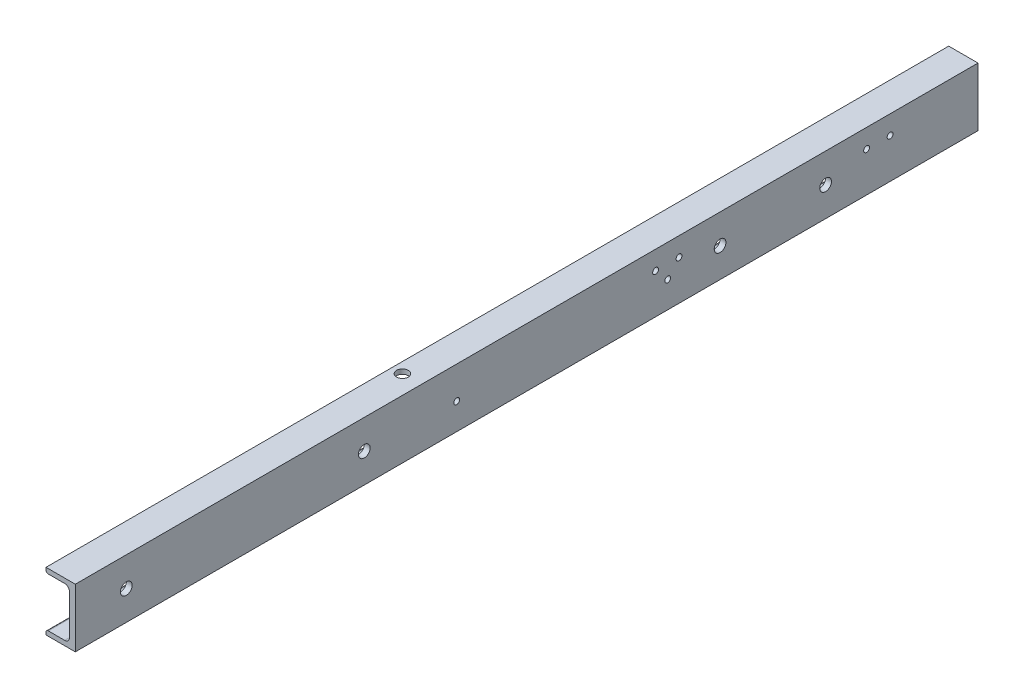
SolidWorks part; units mm, degrees
material "Cast Alloy Steel"
ref_plane "Front Plane" through (0, 0, 0) normal (0, 0, 1) x (1, 0, 0)
ref_plane "Top Plane" through (0, 0, 0) normal (0, 1, 0) x (1, 0, 0)
ref_plane "Right Plane" through (0, 0, 0) normal (1, 0, 0) x (0, 0, -1)
sketch "Sketch4" plane through (0, 0, 0) normal (0, 1, 0) x (1, 0, 0)
  line L0 (0, 0) -> (0, 770)
  dimension "D1" = 770
other "Structural Member1"
ref_plane "Plane1" through (0, 0, 0) normal (0, 0, -1) x (-1, 0, 0)
sketch "Sketch11" plane through (0, 0, 0) normal (0, 0, -1) x (-1, 0, 0)
  line L0 (25, 50) -> (0, 50)
  line L1 (25, 0) -> (0, 0)
  line L2 (0, 50) -> (0, 0)
  line L6 (25, 50) -> (25, 48)
  line L7 (25, 0) -> (25, 2)
  line L12 (5, 42) -> (5, 8)
  line L17 (9, 46) -> (23, 46)
  line L18 (9, 4) -> (23, 4)
  arc A0 (23, 46) -> (25, 48) centre (23, 48) ccw
  arc A1 (23, 4) -> (25, 2) centre (23, 2) cw
  arc A9 (5, 8) -> (9, 4) centre (9, 8) ccw
  arc A10 (5, 42) -> (9, 46) centre (9, 42) cw
  point P8 (0, 25)
  point P9 (5, 25)
  point P10 (12.5, 50)
  point P11 (12.5, 0)
  point P12 (25, 4)
  point P13 (25, 46)
  point P14 (0, 0)
  dimension "D4" = 2
  dimension "RI" = 4
  dimension "D2" = 0
  dimension "D3" = 8
  dimension "Depth" = 50
  dimension "BF" = 25
  dimension "TW" = 5
  dimension "d1" = 34
ref_plane "Plane2" through (0, 25, 0) normal (0, 1, 0) x (-1, 0, 0)
sketch "Sketch14" plane through (0, 0, 0) normal (1, 0, 0) x (0, 0, -1)
  line L0 (595, 78.1737) -> (595, -30.1088) construction
  line L1 (770, 50) -> (770, 0) construction
  dimension "D1" = 175
hole_wizard "Ø10.0 (10) Diameter Hole1" positions "Sketch20" profile "Sketch19" hole size "Ø10.0" standard "ISO"
sketch "Sketch20" plane through (0, 0, 0) normal (1, 0, 0) x (0, 0, -1)
  line L0 (13.75, 25) -> (-13.75, 25) construction
  line L1 (595, 78.1737) -> (595, -30.1088) construction
  point P0 (550, 25)
  point P1 (640, 25)
  dimension "D1" = 0
  dimension "D2" = 0
  dimension "D3" = 90
  dimension "D4" = 45
sketch "Sketch19" plane through (0, 25, -550) normal (0, 1, 0) x (0, 0, -1)
  line L0 (0, 0) -> (0, 14.0043)
  line L1 (0, 14.0043) -> (5, 11)
  line L2 (5, 11) -> (5, 0)
  line L5 (5, 0) -> (0, 0)
  line L10 (0, 14.0043) -> (-5, 11) construction
  line L11 (0, -6.35) -> (0, 107.95) construction
  dimension "Hole Dia." = 10
  dimension "Hole Depth" = 11
  dimension "Drill Angle" = 118
sketch "Sketch21" plane through (0, 0, 0) normal (1, 0, 0) x (0, 0, -1)
  line L0 (145, 120.8048) -> (145, -64.4691) construction
  line L1 (595, 78.1737) -> (595, -30.1088) construction
  dimension "D1" = 450
sketch "Sketch28" plane through (0, 0, 0) normal (0, -1, 0) x (1, 0, 0)
  line L0 (-25, -770) -> (-25, 0) construction
  circle A0 centre (-16, -295) radius 5
  dimension "D1" = 10
  dimension "D2" = 9
  dimension "D3" = 150
extrude "Cut-Extrude1" cut sketch "Sketch28" against normal through all
hole_wizard "Ø10.0 (10) Diameter Hole2" positions "Sketch30" profile "Sketch29" hole size "Ø10.0" standard "ISO"
sketch "Sketch30" plane through (0, 0, 0) normal (1, 0, 0) x (0, 0, -1)
  line L0 (13.75, 25) -> (-13.75, 25) construction
  line L1 (145, 120.8048) -> (145, -64.4691) construction
  point P0 (43.5, 25)
  point P1 (246.5, 25)
  dimension "D1" = 0
  dimension "D2" = 0
  dimension "D3" = 203
  dimension "D4" = 101.5
sketch "Sketch29" plane through (0, 25, -43.5) normal (0, 1, 0) x (0, 0, -1)
  line L0 (0, 0) -> (0, 14.0043)
  line L1 (0, 14.0043) -> (5, 11)
  line L2 (5, 11) -> (5, 0)
  line L5 (5, 0) -> (0, 0)
  line L10 (0, 14.0043) -> (-5, 11) construction
  line L11 (0, -6.35) -> (0, 107.95) construction
  dimension "Hole Dia." = 10
  dimension "Hole Depth" = 11
  dimension "Drill Angle" = 118
hole_wizard "Ø5.0 (5) Diameter Hole1" positions "Sketch32" profile "Sketch31" hole size "Ø5.0" standard "ISO"
sketch "Sketch32" plane through (0, 0, 0) normal (1, 0, 0) x (0, 0, -1)
  line L0 (13.75, 25) -> (-13.75, 25) construction
  circle A0 centre (550, 25) radius 5 construction
  circle A1 centre (640, 25) radius 5 construction
  point P0 (515, 33.95)
  point P1 (675, 33.95)
  point P10 (495, 33.95)
  point P12 (695, 33.95)
  dimension "D1" = 35
  dimension "D2" = 35
  dimension "D3" = 8.95
  dimension "D4" = 8.95
  dimension "D5" = 20
  dimension "D6" = 20
sketch "Sketch31" plane through (0, 33.95, -515) normal (0, 1, 0) x (0, 0, -1)
  line L0 (0, 0) -> (0, 12.5022)
  line L1 (0, 12.5022) -> (2.5, 11)
  line L2 (2.5, 11) -> (2.5, 0)
  line L5 (2.5, 0) -> (0, 0)
  line L10 (0, 12.5022) -> (-2.5, 11) construction
  line L11 (0, -6.35) -> (0, 107.95) construction
  dimension "Hole Dia." = 5
  dimension "Hole Depth" = 11
  dimension "Drill Angle" = 118
sketch "Sketch33" plane through (0, 0, 0) normal (1, 0, 0) x (0, 0, -1)
  circle A0 centre (505.3099, 22.5) radius 2.5
  circle A1 centre (325.3099, 22.5) radius 2.5
  dimension "D1" = 5
  dimension "D2" = 5
extrude "Cut-Extrude2" cut sketch "Sketch33" against normal blind 10
